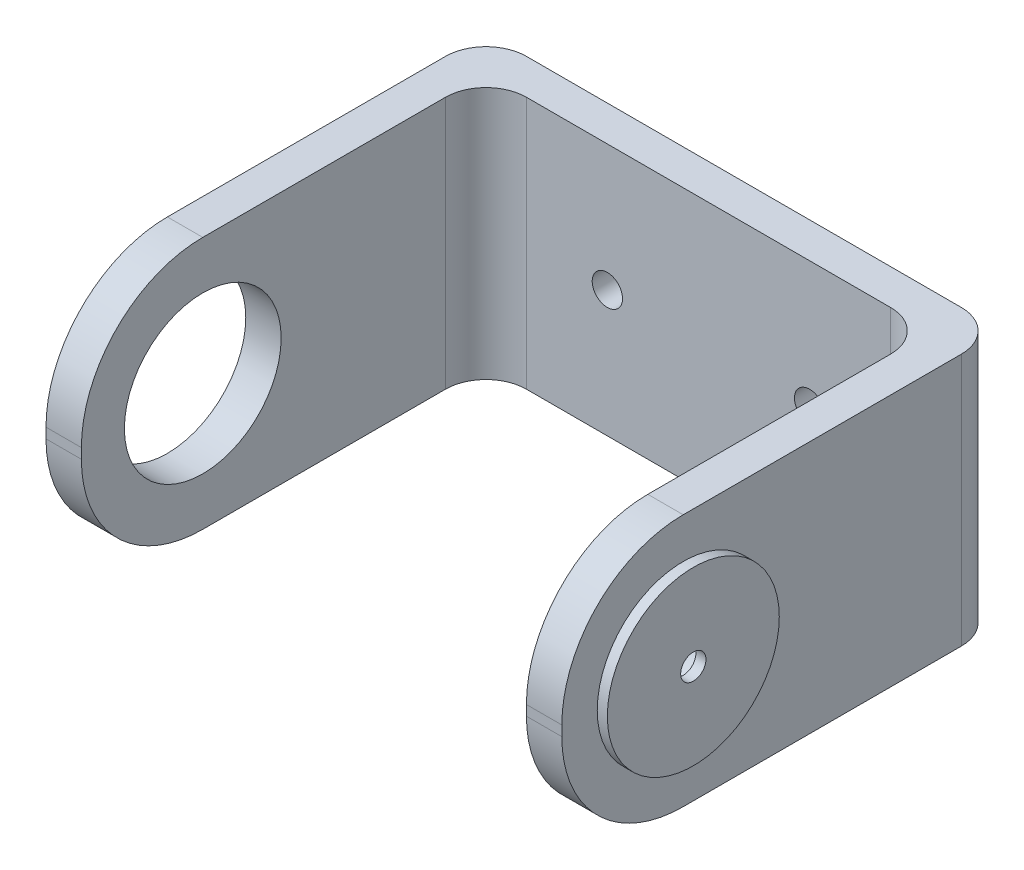
SolidWorks part; units mm, degrees
ref_plane "Alzado" through (0, 0, 0) normal (0, 0, 1) x (1, 0, 0)
ref_plane "Planta" through (0, 0, 0) normal (0, 1, 0) x (1, 0, 0)
ref_plane "Vista lateral" through (0, 0, 0) normal (1, 0, 0) x (0, 0, -1)
sketch "Croquis1" plane through (0, 0, 0) normal (0, 1, 0) x (1, 0, 0)
  line L0 (-22, 0) -> (22, 0)
  line L1 (22, 0) -> (-2.7446, 0)
  line L2 (22, 0) -> (22, -40)
  line L3 (22, -40) -> (25.5, -40)
  line L4 (25.5, -40) -> (25.5, 3.5)
  line L5 (25.5, 3.5) -> (-25.5, 3.5)
  line L6 (-25.5, 3.5) -> (-25.5, -40)
  line L7 (-25.5, -40) -> (-22, -40)
  line L8 (-22, -40) -> (-22, 0)
  point P4 (0, 0)
  dimension "D1" = 44
  dimension "D2" = 3.5
  dimension "D3" = 3.5
  dimension "D4" = 3.5
  dimension "D5" = 40
  dimension "D6" = 40
extrude "Saliente-Extruir1" add sketch "Croquis1" along normal blind 25 contours L7 L8 L0 L2 L3 L4 L5 L6
fillet "Redondeo1" radius 12 4 edges at (23.75, 25, 40) (23.75, 0, 40) (-23.75, 0, 40) (-23.75, 25, 40)
sketch "Croquis2" plane through (-25.5, 0, 0) normal (-1, 0, 0) x (0, 0, 1)
  line L0 (28, 25) -> (28, 0) construction
  arc A0 (40, 13) -> (28, 25) centre (28, 13) ccw construction
  circle A1 centre (28, 12.5) radius 7.75
  dimension "D1" = 15.5
extrude "Cortar-Extruir1" cut sketch "Croquis2" against normal blind 10
sketch "Croquis3" plane through (25.5, 0, 0) normal (1, 0, 0) x (0, 0, -1)
  line L0 (-28, 25) -> (-28, 0) construction
  circle A0 centre (-28, 12.5) radius 2.8
  dimension "D1" = 5.6
extrude "Cortar-Extruir2" cut sketch "Croquis3" against normal blind 10
sketch "Croquis4" plane through (25.5, 0, 0) normal (1, 0, 0) x (0, 0, -1)
  circle A0 centre (-28, 12.5) radius 8.5
  dimension "D1" = 17
extrude "Saliente-Extruir3" add sketch "Croquis4" along normal blind 1
sketch "Croquis5" plane through (26.5, 0, 0) normal (1, 0, 0) x (0, 0, -1)
  circle A0 centre (-28, 12.5) radius 1.25
  dimension "D1" = 2.5
extrude "Cortar-Extruir3" cut sketch "Croquis5" against normal blind 1
fillet "Redondeo2" radius 4 2 edges at (22, 12.5, 0) (-22, 12.5, 0)
fillet "Redondeo3" radius 4 2 edges at (-25.5, 12.5, -3.5) (25.5, 12.5, -3.5)
sketch "Croquis6" plane through (0, 0, -3.5) normal (0, 0, -1) x (-1, 0, 0)
  line L0 (0, 25) -> (0, 0) construction
  line L1 (-21.5, 25) -> (21.5, 25) construction
  line L2 (0, 12.5) -> (-10, 12.5) construction
  line L3 (0, 12.5) -> (10, 12.5) construction
  circle A0 centre (-10, 12.5) radius 1.5
  circle A1 centre (10, 12.5) radius 1.5
  dimension "D3" = 3
  dimension "D4" = 3
  dimension "D1" = 10
  dimension "D2" = 10
extrude "Cortar-Extruir4" cut sketch "Croquis6" against normal blind 10
